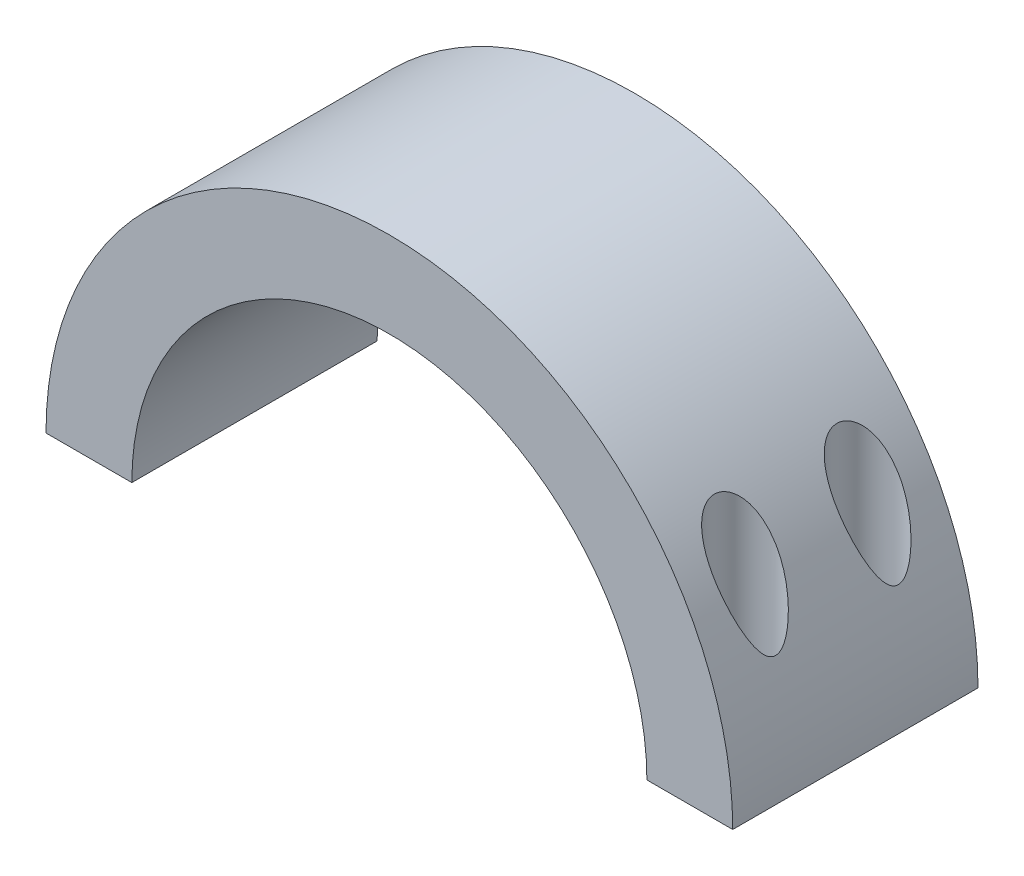
SolidWorks part; units mm, degrees
ref_plane "前视基准面" through (0, 0, 0) normal (0, 0, 1) x (1, 0, 0)
ref_plane "上视基准面" through (0, 0, 0) normal (0, 1, 0) x (1, 0, 0)
ref_plane "右视基准面" through (0, 0, 0) normal (1, 0, 0) x (0, 0, -1)
sketch "草图1" plane through (0, 0, 0) normal (0, 0, 1) x (1, 0, 0)
  line L0 (-28, 0) -> (-21, 0)
  line L1 (21, 0) -> (28, 0)
  arc A0 (21, 0) -> (-21, 0) centre (0, 0) ccw
  arc A1 (28, 0) -> (-28, 0) centre (0, 0) ccw
  dimension "D1" = 42
  dimension "D2" = 56
extrude "凸台-拉伸1" add sketch "草图1" along normal blind 20
sketch "草图2" plane through (0, 0, 0) normal (0, -1, 0) x (1, 0, 0)
  line L0 (-28, 20) -> (-28, 0) construction
  line L1 (-28, 0) -> (-21, 0) construction
  line L2 (-28, 20) -> (-21, 20) construction
  circle A0 centre (-24, 5) radius 1.5
  circle A1 centre (-24, 15) radius 1.5
  dimension "D1" = 3
  dimension "D2" = 3
  dimension "D3" = 4
  dimension "D4" = 5
  dimension "D5" = 5
  dimension "D6" = 4
extrude "切除-拉伸1" cut sketch "草图2" against normal blind 20
mirror "镜向1" about plane through (0, 0, 0) normal (1, 0, 0) of "切除-拉伸1"
ref_plane "基准面1" through (0, 5, 0) normal (0, -1, 0) x (-1, 0, 0)
sketch "草图3" plane through (0, 5, 0) normal (0, -1, 0) x (-1, 0, 0)
  circle A0 centre (24, -5) radius 2.5
  circle A1 centre (24, -15) radius 2.5
  dimension "D1" = 5
  dimension "D2" = 5
extrude "切除-拉伸2" cut sketch "草图3" against normal blind 20
mirror "镜向2" about plane through (0, 0, 0) normal (1, 0, 0) of "切除-拉伸2"
